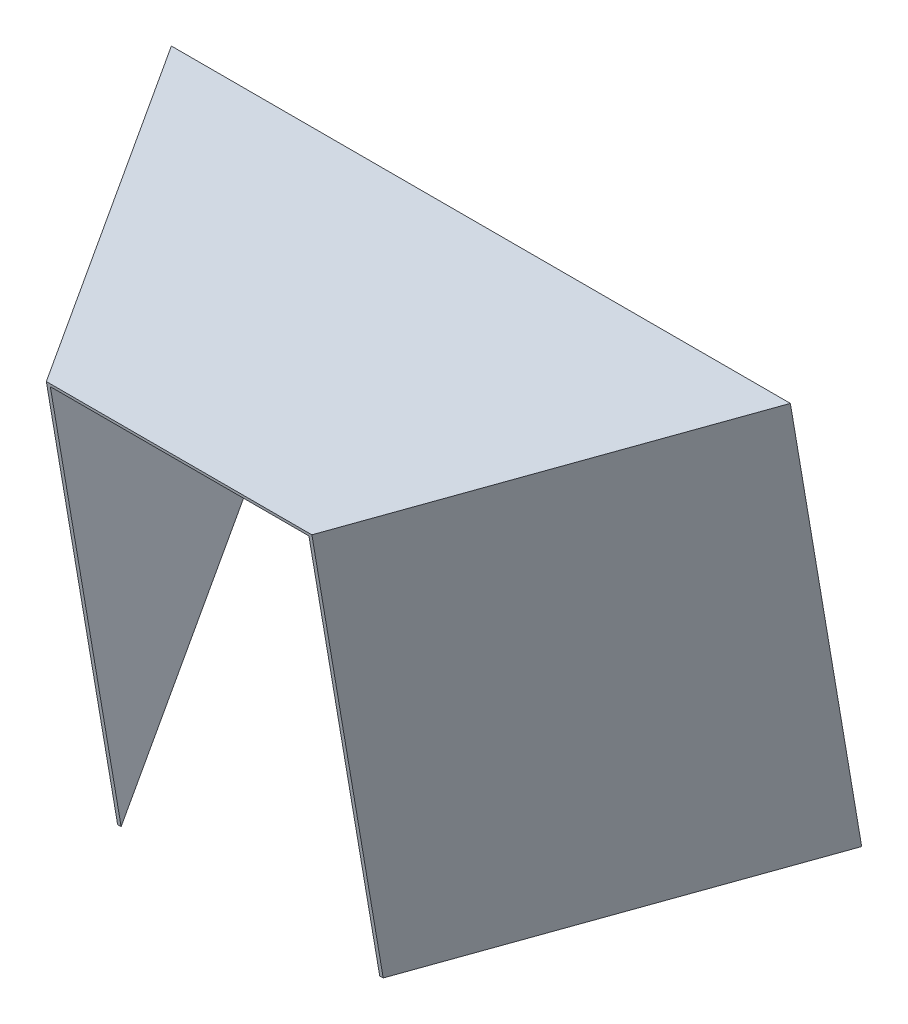
SolidWorks part; units mm, degrees
ref_plane "Front Plane" through (0, 0, 0) normal (0, 0, 1) x (1, 0, 0)
ref_plane "Top Plane" through (0, 0, 0) normal (0, 1, 0) x (1, 0, 0)
ref_plane "Right Plane" through (0, 0, 0) normal (1, 0, 0) x (0, 0, -1)
sketch "Sketch3" plane through (0, 0, 0) normal (1, 0, 0) x (0, 0, -1)
  line L0 (0, 0) -> (635, 0)
  line L1 (0, 0) -> (0, 501.65)
  line L2 (635, 0) -> (635, 609.6)
  line L3 (635, 609.6) -> (0, 501.65)
  dimension "D1" = 609.6
  dimension "D2" = 635
  dimension "D3" = 501.65
extrude "Boss-Extrude1" add sketch "Sketch3" along normal blind 6.35
sketch "Sketch5" plane through (0, 487.5595, 82.8851) normal (0, 0.9859, 0.1676) x (1, 0, 0)
  line L0 (6.35, 84.0743) -> (378.2273, 728.1847)
  line L1 (6.35, 84.0743) -> (-552.45, 84.0743)
  line L5 (378.2273, 728.1847) -> (-924.3273, 728.1847)
  line L6 (-552.45, 84.0743) -> (-924.3273, 728.1847)
  line L7 (6.35, 728.1847) -> (0, 728.1847) construction
  dimension "D1" = 558.8
  dimension "D2" = 120
  dimension "D3" = 120
extrude "Boss-Extrude2" add sketch "Sketch5" along normal blind 6.35
sketch "Sketch10" plane through (6.35, 0, 0) normal (1, 0, 0) x (0, 0, -1)
  line L4 (0, 501.65) -> (0, 0)
  line L5 (0, 0) -> (635, 0)
  line L6 (635, 0) -> (635, 609.6)
  line L7 (635, 609.6) -> (0, 501.65)
  line L8 (0, 501.65) -> (0, 0)
  line L9 (0, 0) -> (635, 0)
  line L10 (635, 0) -> (635, 609.6)
  line L11 (635, 609.6) -> (0, 501.65)
  dimension "D1" = 0
extrude "Cut-Extrude2" cut sketch "Sketch10" against normal up to next
sketch "Sketch9" plane through (0, 487.5595, 82.8851) normal (0, -0.9859, -0.1676) x (1, 0, 0)
  line L0 (378.2273, -728.1847) -> (6.35, -84.0743)
  line L1 (6.35, -84.0743) -> (-0.9823, -84.0743)
  line L2 (-0.9823, -84.0743) -> (370.895, -728.1847)
  line L3 (378.2273, -728.1847) -> (-924.3273, -728.1847) construction
  line L4 (370.895, -728.1847) -> (378.2273, -728.1847)
  line L5 (-924.3273, -728.1847) -> (-552.45, -84.0743)
  line L8 (-552.45, -84.0743) -> (-545.1177, -84.0743)
  line L9 (-545.1177, -84.0743) -> (-916.995, -728.1847)
  line L10 (378.2273, -728.1847) -> (-924.3273, -728.1847) construction
  line L11 (-916.995, -728.1847) -> (-924.3273, -728.1847)
  line L12 (6.35, -84.0743) -> (-552.45, -84.0743) construction
  dimension "D1" = 6.35
  dimension "D2" = 6.35
extrude "Boss-Extrude3" add sketch "Sketch9" along normal blind 889
